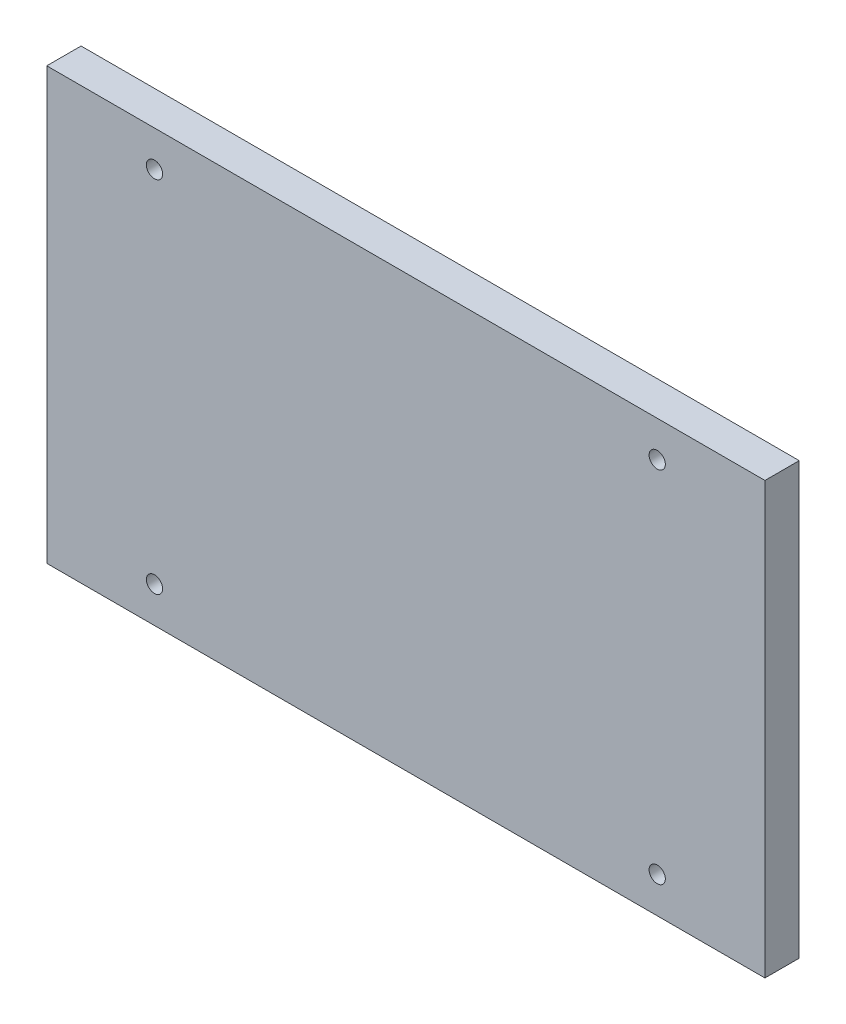
SolidWorks part; units mm, degrees
ref_plane "Front Plane" through (0, 0, 0) normal (0, 0, 1) x (1, 0, 0)
ref_plane "Top Plane" through (0, 0, 0) normal (0, 1, 0) x (1, 0, 0)
ref_plane "Right Plane" through (0, 0, 0) normal (1, 0, 0) x (0, 0, -1)
sketch "Sketch1" plane through (0, 0, 0) normal (0, 0, 1) x (1, 0, 0)
  line L13 (15, -5) -> (85, -5) construction
  line L14 (15, -5) -> (15, -55) construction
  line L15 (15, -55) -> (85, -55) construction
  line L16 (85, -5) -> (85, -55) construction
  line L17 (0, 0) -> (100, 0)
  line L18 (0, 0) -> (0, -60)
  line L19 (0, -60) -> (100, -60)
  line L20 (100, 0) -> (100, -60)
  circle A8 centre (15, -5) radius 1.13
  circle A9 centre (15, -55) radius 1.13
  circle A10 centre (85, -5) radius 1.13
  circle A11 centre (85, -55) radius 1.13
  dimension "D7" = 2.26
  dimension "D13" = 70
  dimension "D2" = 100
  dimension "D3" = 50
  dimension "D4" = 60
  dimension "D5" = 5
  dimension "D6" = 15
extrude "Boss-Extrude1" add sketch "Sketch1" along normal blind 4.7752
hole_wizard "#4-40 Tapped Hole1" positions "3DSketch1" profile "Sketch2" tap size "#4-40" standard "ANSI Inch" end condition through all
sketch3d "3DSketch1"
  line L0 (15, -5, 4.7752) -> (15, -5, 0) construction
  line L1 (85, -5, 4.7752) -> (85, -5, 0) construction
  line L2 (85, -55, 4.7752) -> (85, -55, 0) construction
  line L3 (15, -55, 4.7752) -> (15, -55, 0) construction
  point P0 (15, -5, 4.7752)
  point P2 (15, -55, 4.7752)
  point P4 (85, -55, 4.7752)
  point P6 (85, -5, 4.7752)
sketch "Sketch2" plane through (15, -5, 4.7752) normal (1, 0, 0) x (0, -1, 0)
  line L0 (0, 0) -> (0, 4.7752)
  line L1 (0, 4.7752) -> (1.1303, 4.7752)
  line L2 (1.1303, 4.7752) -> (1.1303, 0)
  line L5 (1.1303, 0) -> (0, 0)
  line L11 (0, -6.35) -> (0, 107.95) construction
  dimension "Thru Tap Drill Dia." = 2.2606
  dimension "Thru Tap Drill Depth" = 4.7752
cosmetic thread "Hole Thread1"
cosmetic thread "Hole Thread2"
cosmetic thread "Hole Thread3"
cosmetic thread "Hole Thread4"
equation "\"D6@Sketch1\"=(\"D2@Sketch1\"-\"D13@Sketch1\")/2"
